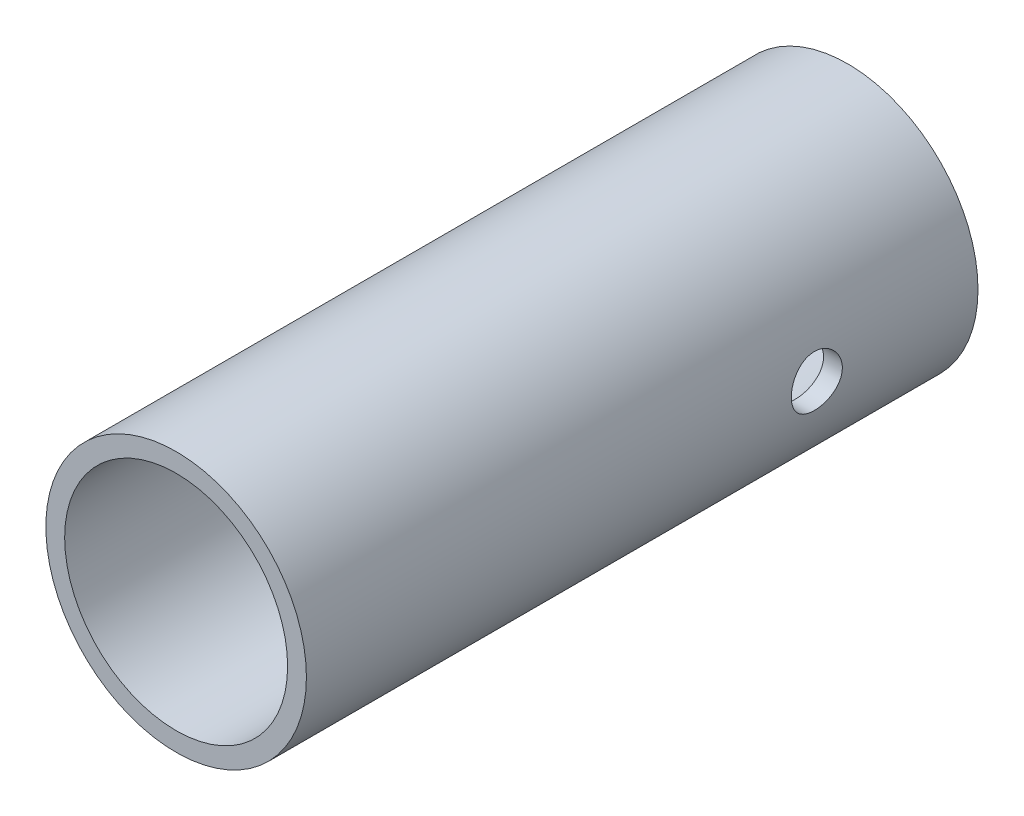
SolidWorks part; units mm, degrees
ref_plane "Front Plane" through (0, 0, 0) normal (0, 0, 1) x (1, 0, 0)
ref_plane "Top Plane" through (0, 0, 0) normal (0, 1, 0) x (1, 0, 0)
ref_plane "Right Plane" through (0, 0, 0) normal (1, 0, 0) x (0, 0, -1)
sketch "Sketch1" plane through (0, 0, 0) normal (0, 0, 1) x (1, 0, 0)
  circle A0 centre (0, 0) radius 4.85
  dimension "D1" = 9.7
extrude "Boss-Extrude1" add sketch "Sketch1" along normal blind 25
sketch "Sketch2" plane through (0, 0, 25) normal (0, 0, 1) x (1, 0, 0)
  circle A0 centre (0, 0) radius 4.15
  dimension "D1" = 8.3
extrude "Cut-Extrude1" cut sketch "Sketch2" against normal through all
sketch "Sketch3" plane through (0, 0, 0) normal (1, 0, 0) x (0, 0, -1)
  line L0 (-6, 0) -> (0, 0) construction
  circle A0 centre (-6, 0) radius 0.95
  dimension "D1" = 1.9
  dimension "D2" = 6
extrude "Cut-Extrude2" cut sketch "Sketch3" against normal through all both and the other way through all
